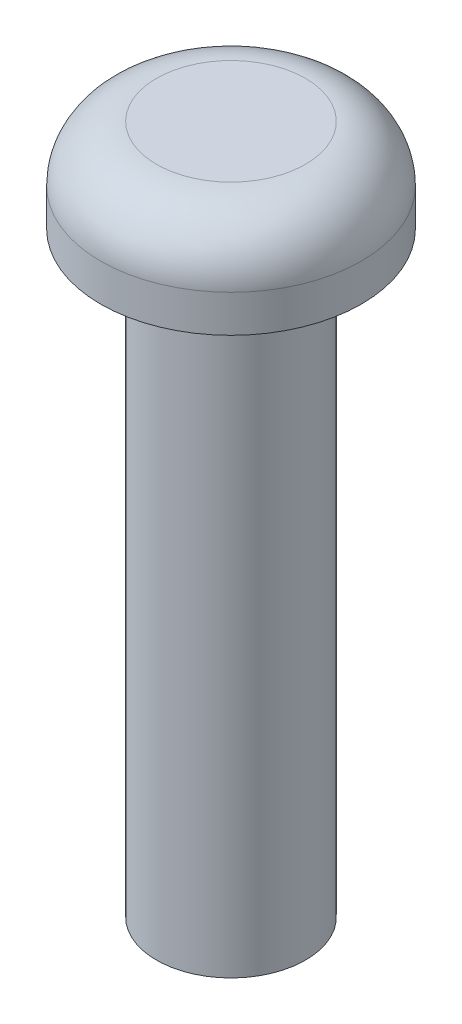
SolidWorks part; units mm, degrees
ref_plane "Front Plane" through (0, 0, 0) normal (0, 0, 1) x (1, 0, 0)
ref_plane "Top Plane" through (0, 0, 0) normal (0, 1, 0) x (1, 0, 0)
ref_plane "Right Plane" through (0, 0, 0) normal (1, 0, 0) x (0, 0, -1)
sketch "Sketch1" plane through (0, 0, 0) normal (0, 0, 1) x (1, 0, 0)
  line L0 (2, 0) -> (3.5, 0)
  line L1 (3.5, 0) -> (3.5, 1)
  line L2 (2, 2.5) -> (0, 2.5)
  line L3 (2, 0) -> (2, -16)
  line L4 (2, -16) -> (0, -16)
  line L5 (0, -16) -> (0, 2.5)
  arc A0 (3.5, 1) -> (2, 2.5) centre (2, 1) ccw
  dimension "D1" = 2
  dimension "D2" = 16
  dimension "D3" = 3.5
  dimension "D4" = 2.5
revolve "Revolve1" add sketch "Sketch1" angle 360 about L5
